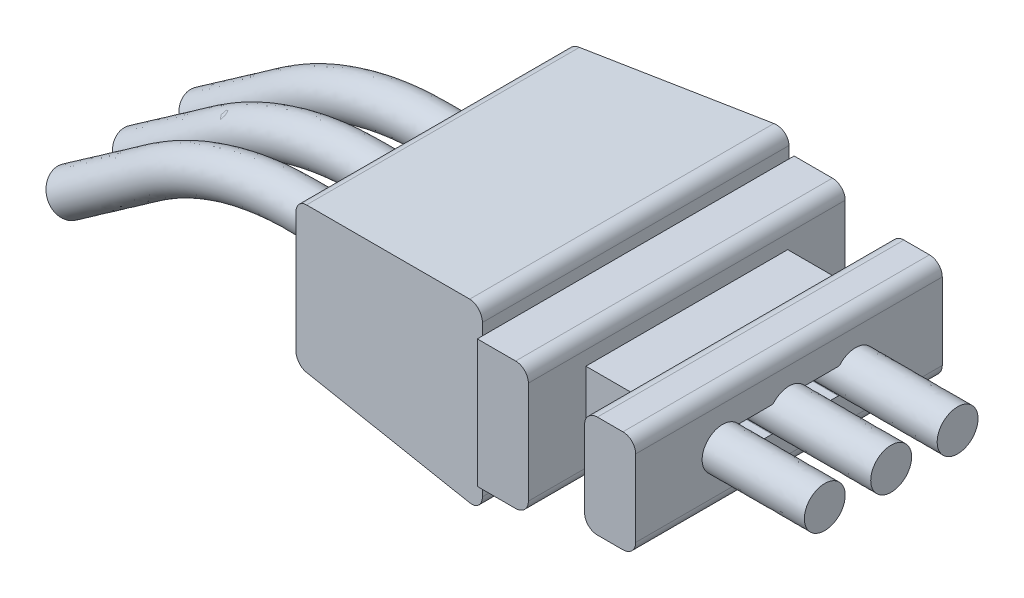
SolidWorks part; units mm, degrees
material "Rubber"
ref_plane "Front Plane" through (0, 0, 0) normal (0, 0, 1) x (1, 0, 0)
ref_plane "Top Plane" through (0, 0, 0) normal (0, 1, 0) x (1, 0, 0)
ref_plane "Right Plane" through (0, 0, 0) normal (1, 0, 0) x (0, 0, -1)
sketch "Sketch1" plane through (0, 0, 0) normal (1, 0, 0) x (0, 0, -1)
  line L1 (-3, 1) -> (3, 1)
  line L2 (-3, 1) -> (-3, -1)
  line L3 (-3, -1) -> (3, -1)
  line L4 (3, 1) -> (3, -1)
  line L5 (-3, 1) -> (3, -1) construction
  line L6 (-3, -1) -> (3, 1) construction
  point P0 (0, 0)
  dimension "D1" = 6
  dimension "D2" = 2
extrude "Boss-Extrude1" add sketch "Sketch1" along normal blind 1
sketch "Sketch2" plane through (0, 0, 0) normal (-1, 0, 0) x (0, 0, 1)
  line L1 (1.975, -0.725) -> (-1.975, -0.725)
  line L2 (1.975, -0.725) -> (1.975, 0.725)
  line L3 (1.975, 0.725) -> (-1.975, 0.725)
  line L4 (-1.975, -0.725) -> (-1.975, 0.725)
  line L5 (1.975, -0.725) -> (-1.975, 0.725) construction
  line L6 (1.975, 0.725) -> (-1.975, -0.725) construction
  point P0 (0, 0)
  dimension "D1" = 3.95
  dimension "D2" = 1.45
extrude "Boss-Extrude2" add sketch "Sketch2" along normal blind 1
sketch "Sketch3" plane through (-1, 0, 0) normal (-1, 0, 0) x (0, 0, 1)
  line L1 (3.1, -1.25) -> (-3.1, -1.25)
  line L2 (3.1, -1.25) -> (3.1, 1.25)
  line L3 (3.1, 1.25) -> (-3.1, 1.25)
  line L4 (-3.1, -1.25) -> (-3.1, 1.25)
  line L5 (3.1, -1.25) -> (-3.1, 1.25) construction
  line L6 (3.1, 1.25) -> (-3.1, -1.25) construction
  point P0 (0, 0)
  dimension "D1" = 6.2
  dimension "D2" = 2.5
extrude "Boss-Extrude3" add sketch "Sketch3" along normal blind 1
sketch "Sketch4" plane through (-2, 0, 0) normal (-1, 0, 0) x (0, 0, 1)
  line L1 (3, -1.75) -> (-3, -1.75)
  line L2 (3, -1.75) -> (3, 1.75)
  line L3 (3, 1.75) -> (-3, 1.75)
  line L4 (-3, -1.75) -> (-3, 1.75)
  line L5 (3, -1.75) -> (-3, 1.75) construction
  line L6 (3, 1.75) -> (-3, -1.75) construction
  point P0 (0, 0)
  dimension "D1" = 6
  dimension "D2" = 3.5
extrude "Boss-Extrude4" add sketch "Sketch4" along normal blind 4 draft 5
fillet "Fillet2" radius 0.25 10 edges at (1, 1, 0) (0, 1, 0) (1, -1, 0) (0, -1, 0) (-6, 1.4, 0) (-1, 1.25, 0) (-6, -1.4, 0) (-1, -1.25, 0) (-2, 1.75, 0) (-2, -1.75, 0)
sketch "Sketch15" plane through (-6, 0, 0) normal (-1, 0, 0) x (0, 0, 1)
  line L0 (0, 0) -> (1.3, 0) construction
  line L1 (0, 0) -> (-1.3, 0) construction
  line L2 (-0.9646, 0.25) -> (-0.3354, 0.25)
  line L3 (-0.9646, -0.25) -> (-0.3354, -0.25)
  line L4 (0.3354, -0.25) -> (0.9646, -0.25)
  line L5 (0.3354, 0.25) -> (0.9646, 0.25)
  arc A0 (0.2981, 0.2667) -> (-0.2981, 0.2667) centre (0, 0) ccw
  arc A1 (1.0019, -0.2667) -> (1.0019, 0.2667) centre (1.3, 0) ccw
  arc A2 (-1.0019, 0.2667) -> (-1.0019, -0.2667) centre (-1.3, 0) ccw
  arc A3 (-0.2981, -0.2667) -> (0.2981, -0.2667) centre (0, 0) ccw
  arc A4 (0.9646, -0.25) -> (1.0019, -0.2667) centre (0.9646, -0.3) cw
  arc A5 (0.2981, -0.2667) -> (0.3354, -0.25) centre (0.3354, -0.3) cw
  arc A6 (0.2981, 0.2667) -> (0.3354, 0.25) centre (0.3354, 0.3) ccw
  arc A7 (0.9646, 0.25) -> (1.0019, 0.2667) centre (0.9646, 0.3) ccw
  arc A8 (-0.3354, -0.25) -> (-0.2981, -0.2667) centre (-0.3354, -0.3) cw
  arc A9 (-0.9646, -0.25) -> (-1.0019, -0.2667) centre (-0.9646, -0.3) ccw
  arc A10 (-0.3354, 0.25) -> (-0.2981, 0.2667) centre (-0.3354, 0.3) ccw
  arc A11 (-0.9646, 0.25) -> (-1.0019, 0.2667) centre (-0.9646, 0.3) cw
  point P20 (0.3122, -0.25)
  point P23 (0.3122, 0.25)
  point P28 (-0.3122, -0.25)
  dimension "D1" = 0.8
  dimension "D7" = 0.05
  dimension "D3" = 1.3
  dimension "D5" = 1.3
  dimension "D6" = 0.5
  dimension "D2" = 2
  dimension "D4" = 2
extrude "Cut-Extrude6" cut sketch "Sketch15" against normal through all
sketch "Sketch10" plane through (0, 0, 0) normal (0, 0, 1) x (1, 0, 0)
  line L0 (1, 0) -> (-7.2735, 0)
  line L2 (1, -0.2667) -> (1, -0.25) construction
  line L3 (-10.1414, -0.9042) -> (-11.7797, -2.0514)
  line L4 (1, 0) -> (3, 0)
  arc A0 (-7.2735, 0) -> (-10.1414, -0.9042) centre (-7.2735, -5) ccw
  point P5 (0, 0)
  point P11 (0, 0)
  dimension "D3" = 5
  dimension "D2" = 145
  dimension "D4" = 2
  dimension "D5" = 2
sweep "Sweep3" add path "Sketch10" circular profile diameter 0.8 parameters "D3"=0.8
pattern_linear "LPattern1" count 2 spacing 1.3 along (0, 0, 1) count 2 spacing 1.3 along (0, 0, -1) of "Sweep3"
